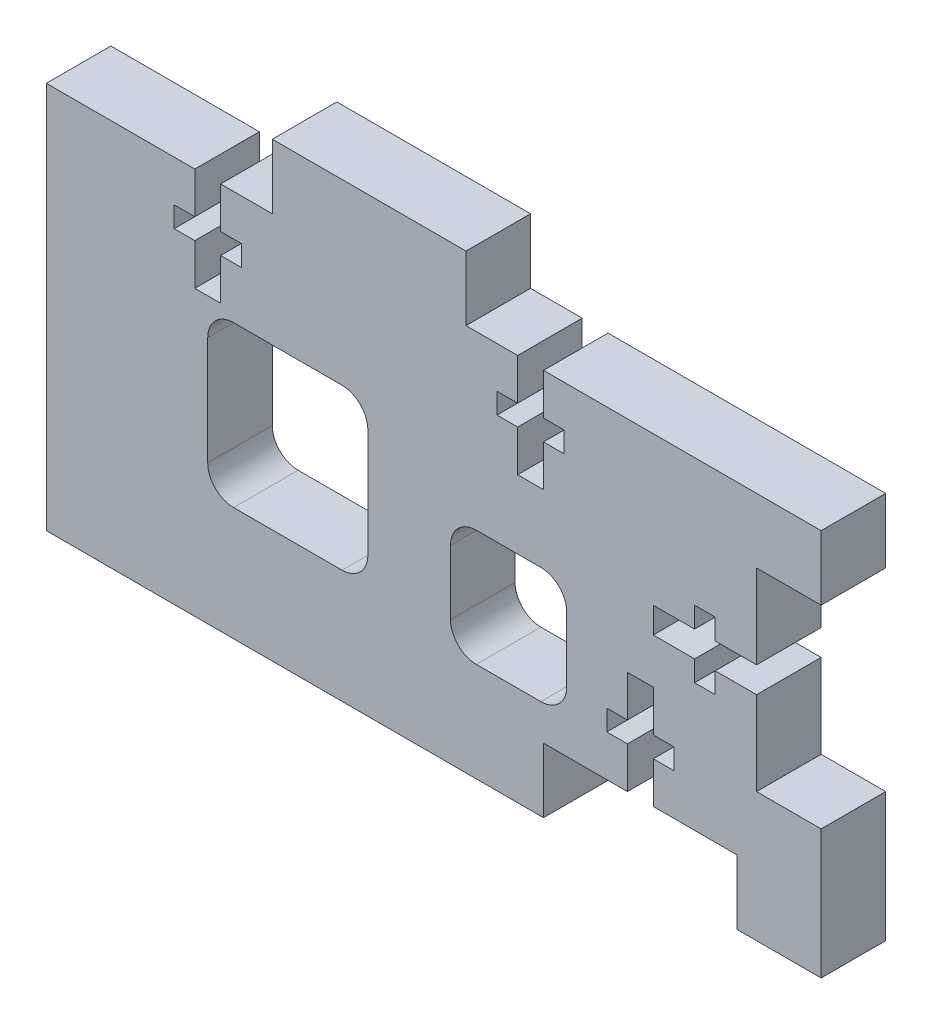
SolidWorks part; units mm, degrees
ref_plane "Front" through (0, 0, 0) normal (0, 0, 1) x (1, 0, 0)
ref_plane "Top" through (0, 0, 0) normal (0, 1, 0) x (1, 0, 0)
ref_plane "Right" through (0, 0, 0) normal (1, 0, 0) x (0, 0, -1)
sketch "Sketch1" plane through (0, 0, 0) normal (0, 0, 1) x (1, 0, 0)
  line L1 (-38.1, -15.875) -> (38.1, -15.875)
  line L2 (-38.1, -15.875) -> (-38.1, 15.875)
  line L3 (-38.1, 15.875) -> (38.1, 15.875)
  line L4 (38.1, -15.875) -> (38.1, 15.875)
  line L5 (-38.1, -15.875) -> (38.1, 15.875) construction
  line L6 (-38.1, 15.875) -> (38.1, -15.875) construction
  point P0 (0, 0)
  dimension "D1" = 31.75
  dimension "D2" = 76.2
extrude "Boss-Extrude1" add sketch "Sketch1" along normal blind 6.35
sketch "Sketch2" plane through (0, 0, 6.35) normal (0, 0, 1) x (1, 0, 0)
  line L0 (-38.1, 15.875) -> (-38.1, -15.875) construction
  line L1 (-15.875, 15.875) -> (3.175, 15.875)
  line L2 (-15.875, 15.875) -> (-15.875, 22.225)
  line L3 (-15.875, 22.225) -> (3.175, 22.225)
  line L4 (3.175, 15.875) -> (3.175, 22.225)
  line L5 (-15.875, 15.875) -> (3.175, 22.225) construction
  line L6 (-15.875, 22.225) -> (3.175, 15.875) construction
  line L7 (38.1, 15.875) -> (-38.1, 15.875) construction
  point P0 (-6.35, 19.05)
  dimension "D1" = 19.05
  dimension "D2" = 6.35
  dimension "D3" = 31.75
extrude "Boss-Extrude2" add sketch "Sketch2" against normal up to surface (6.35 mm away) up to face at (0, 0, 0)
sketch "Sketch3" plane through (0, 0, 6.35) normal (0, 0, 1) x (1, 0, 0)
  line L0 (-6.35, 22.225) -> (-6.35, 15.7879) construction
  line L1 (3.175, 22.225) -> (-15.875, 22.225) construction
  line L2 (-15.875, 19.05) -> (3.175, 19.05) construction
  line L3 (-15.875, 22.225) -> (-15.875, 15.875) construction
  line L4 (3.175, 15.875) -> (3.175, 22.225) construction
  line L5 (-20.955, 11.811) -> (-18.923, 11.811)
  line L6 (-23.495, 15.875) -> (-20.955, 15.875)
  line L7 (-23.495, 15.875) -> (-23.495, 11.811)
  line L8 (-23.495, 5.715) -> (-20.955, 5.715)
  line L9 (-20.955, 15.875) -> (-20.955, 11.811)
  line L10 (-23.495, 15.875) -> (-20.955, 5.715) construction
  line L11 (-23.495, 5.715) -> (-20.955, 15.875) construction
  line L12 (-25.527, 9.779) -> (-23.495, 9.779)
  line L13 (-25.527, 9.779) -> (-25.527, 11.811)
  line L14 (-25.527, 11.811) -> (-23.495, 11.811)
  line L15 (-18.923, 9.779) -> (-18.923, 11.811)
  line L16 (-25.527, 9.779) -> (-18.923, 11.811) construction
  line L17 (-25.527, 11.811) -> (-18.923, 9.779) construction
  line L18 (-20.955, 9.779) -> (-18.923, 9.779)
  line L19 (-23.495, 9.779) -> (-23.495, 5.715)
  line L20 (-20.955, 9.779) -> (-20.955, 5.715)
  line L21 (-15.875, 15.875) -> (-38.1, 15.875) construction
  line L22 (12.827, 11.811) -> (6.223, 9.779) construction
  line L23 (12.827, 9.779) -> (6.223, 11.811) construction
  line L24 (10.795, 5.715) -> (8.255, 15.875) construction
  line L25 (10.795, 15.875) -> (8.255, 5.715) construction
  line L26 (8.255, 9.779) -> (8.255, 5.715)
  line L27 (10.795, 9.779) -> (10.795, 5.715)
  line L28 (8.255, 9.779) -> (6.223, 9.779)
  line L29 (6.223, 9.779) -> (6.223, 11.811)
  line L30 (12.827, 11.811) -> (10.795, 11.811)
  line L31 (12.827, 9.779) -> (12.827, 11.811)
  line L32 (12.827, 9.779) -> (10.795, 9.779)
  line L33 (8.255, 15.875) -> (8.255, 11.811)
  line L34 (10.795, 5.715) -> (8.255, 5.715)
  line L35 (10.795, 15.875) -> (10.795, 11.811)
  line L36 (10.795, 15.875) -> (8.255, 15.875)
  line L37 (8.255, 11.811) -> (6.223, 11.811)
  point P10 (-22.225, 10.795)
  point P15 (-22.225, 10.795)
  point P38 (9.525, 10.795)
  dimension "D1" = 2.54
  dimension "D2" = 10.16
  dimension "D3" = 2.032
  dimension "D4" = 6.604
  dimension "D5" = 15.875
extrude "Cut-Extrude1" cut sketch "Sketch3" against normal up to surface (6.35 mm away) up to face at (0.3969, 9.525, 0)
sketch "Sketch4" plane through (0, 0, 6.35) normal (0, 0, 1) x (1, 0, 0)
  line L0 (38.1, -15.875) -> (38.1, 15.875) construction
  line L1 (38.1, 0) -> (-38.1, 0) construction
  line L3 (38.1, -15.875) -> (38.1, 15.875) construction
  line L4 (31.75, -9.525) -> (38.1, -9.525)
  line L5 (31.75, -9.525) -> (31.75, -1.27)
  line L6 (31.75, 9.525) -> (38.1, 9.525)
  line L7 (38.1, -9.525) -> (38.1, 9.525)
  line L8 (31.75, -9.525) -> (38.1, 9.525) construction
  line L9 (31.75, 9.525) -> (38.1, -9.525) construction
  line L10 (25.654, 1.27) -> (21.59, 1.27)
  line L11 (31.75, 1.27) -> (27.686, 1.27)
  line L12 (0, 0) -> (0, 22.225) construction
  line L13 (31.75, -1.27) -> (27.686, -1.27)
  line L14 (21.59, 1.27) -> (21.59, -1.27)
  line L15 (31.75, 1.27) -> (21.59, -1.27) construction
  line L16 (31.75, -1.27) -> (21.59, 1.27) construction
  line L17 (25.654, 3.302) -> (27.686, 3.302)
  line L18 (25.654, 3.302) -> (25.654, 1.27)
  line L19 (25.654, -3.302) -> (27.686, -3.302)
  line L20 (27.686, 3.302) -> (27.686, 1.27)
  line L21 (25.654, 3.302) -> (27.686, -3.302) construction
  line L22 (25.654, -3.302) -> (27.686, 3.302) construction
  line L23 (25.654, -1.27) -> (21.59, -1.27)
  line L24 (25.654, -1.27) -> (25.654, -3.302)
  line L25 (27.686, -1.27) -> (27.686, -3.302)
  line L26 (31.75, 1.27) -> (31.75, 9.525)
  line L27 (3.175, 22.225) -> (-15.875, 22.225) construction
  point P0 (38.1, 0)
  point P7 (34.925, 0)
  point P14 (26.67, 0)
  point P19 (26.67, 0)
  point P40 (-30.4006, -32.6246)
  dimension "D1" = 6.35
  dimension "D2" = 19.05
  dimension "D3" = 2.54
  dimension "D4" = 10.16
  dimension "D5" = 6.604
  dimension "D6" = 2.032
  dimension "D7" = 1.27
extrude "Cut-Extrude4" cut sketch "Sketch4" against normal up to surface (6.35 mm away) up to face at (-4.7427, 10.4775, 0)
sketch "Sketch5" plane through (0, 0, 6.35) normal (0, 0, 1) x (1, 0, 0)
  line L1 (-38.1, -15.875) -> (38.1, -15.875)
  line L2 (-38.1, -15.875) -> (-38.1, -22.225)
  line L3 (-38.1, -22.225) -> (38.1, -22.225)
  line L4 (38.1, -15.875) -> (38.1, -22.225)
  dimension "D1" = 6.35
extrude "Boss-Extrude3" add sketch "Sketch5" against normal up to surface (6.35 mm away) up to face at (6.4161, 6.985, 0)
sketch "Sketch6" plane through (0, 0, 6.35) normal (0, 0, 1) x (1, 0, 0)
  line L0 (-38.1, -22.225) -> (38.1, -22.225) construction
  line L1 (0, -22.225) -> (0, -1.6974) construction
  line L2 (-9.525, -22.225) -> (9.525, -22.225)
  line L3 (-9.525, -22.225) -> (-9.525, -15.875)
  line L4 (-9.525, -15.875) -> (-1.27, -15.875)
  line L5 (9.525, -22.225) -> (9.525, -15.875)
  line L6 (1.27, -15.875) -> (9.525, -15.875)
  line L7 (-1.27, -9.779) -> (-1.27, -5.715)
  line L8 (-1.27, -15.875) -> (-1.27, -11.811)
  line L9 (-1.27, -5.715) -> (1.27, -5.715)
  line L10 (1.27, -15.875) -> (1.27, -11.811)
  line L11 (-1.27, -15.875) -> (1.27, -5.715) construction
  line L12 (-1.27, -5.715) -> (1.27, -15.875) construction
  line L13 (-3.302, -11.811) -> (-1.27, -11.811)
  line L14 (-3.302, -11.811) -> (-3.302, -9.779)
  line L15 (-3.302, -9.779) -> (-1.27, -9.779)
  line L16 (3.302, -11.811) -> (3.302, -9.779)
  line L17 (-3.302, -11.811) -> (3.302, -9.779) construction
  line L18 (-3.302, -9.779) -> (3.302, -11.811) construction
  line L19 (1.27, -11.811) -> (3.302, -11.811)
  line L20 (1.27, -9.779) -> (1.27, -5.715)
  line L21 (1.27, -9.779) -> (3.302, -9.779)
  point P0 (0, -22.225)
  point P10 (0, -10.795)
  point P15 (0, -10.795)
  dimension "D1" = 19.05
  dimension "D2" = 6.35
  dimension "D3" = 9.525
  dimension "D4" = 10.16
  dimension "D5" = 2.54
  dimension "D6" = 2.032
  dimension "D7" = 6.604
extrude "Cut-Extrude5" [suppressed] cut sketch "Sketch6" against normal up to surface (6.35 mm away)
sketch "Sketch7" [suppressed] plane through (0, 0, 6.35) normal (0, 0, 1) x (1, 0, 0)
  line L0 (-3.302, -9.779) -> (-3.302, -11.811) construction
  line L1 (-31.7421, -12.928) -> (31.7421, -12.928) construction
  line L2 (-31.7421, -12.928) -> (-31.7421, 3.175) construction
  line L3 (-31.7421, 12.928) -> (31.7421, 12.928) construction
  line L4 (31.7421, -12.928) -> (31.7421, 12.928) construction
  line L5 (-31.7421, -12.928) -> (31.7421, 12.928) construction
  line L6 (-31.7421, 12.928) -> (31.7421, -12.928) construction
  line L7 (-8.382, -4.4173) -> (8.382, -4.4173)
  line L8 (8.255, 5.715) -> (10.795, 5.715) construction
  line L9 (-23.516, 3.175) -> (16.51, 3.175)
  line L10 (16.51, -2.2291) -> (16.51, 3.175)
  line L11 (-16.3971, -3.1533) -> (16.51, 3.175) construction
  line L12 (-23.516, 3.175) -> (16.51, -2.2291) construction
  line L14 (-31.7421, 3.175) -> (-31.7421, -12.928)
  line L15 (-31.7421, -12.928) -> (-8.382, -12.928)
  line L16 (-8.382, -4.4173) -> (-8.382, -12.928)
  line L17 (16.51, -2.2291) -> (16.51, -12.928)
  line L18 (16.51, -12.928) -> (8.382, -12.928)
  line L19 (8.382, -4.4173) -> (8.382, -12.928)
  line L20 (3.302, -11.811) -> (3.302, -9.779) construction
  line L21 (21.59, 1.27) -> (21.59, -1.27) construction
  line L22 (-23.516, 3.175) -> (-31.7421, 3.175)
  line L23 (-31.7421, 4.7625) -> (-31.7421, 12.928) construction
  point P0 (0, 0)
  point P6 (0, 0)
  point P11 (-31.7421, 4.7625)
  point P12 (-23.516, 3.175)
  dimension "D1" = 9.525
  dimension "D3" = 5.08
  dimension "D4" = 5.08
  dimension "D5" = 5.08
  dimension "D6" = 2.54
extrude "Cut-Extrude6" [suppressed] cut sketch "Sketch7" against normal up to surface (6.35 mm away)
sketch "Sketch8" plane through (0, 0, 6.35) normal (0, 0, 1) x (1, 0, 0)
  line L0 (-38.1, -22.225) -> (38.1, -22.225) construction
  line L1 (-19.685, 4.699) -> (-9.017, 4.699)
  line L2 (-22.225, 2.159) -> (-22.225, -8.509)
  line L3 (-19.685, -11.049) -> (-9.017, -11.049)
  line L4 (-6.477, 2.159) -> (-6.477, -8.509)
  line L5 (4.191, -1.0414) -> (10.541, -1.0414)
  line L6 (1.651, -3.5814) -> (1.651, -9.9314)
  line L7 (4.191, -12.4714) -> (10.541, -12.4714)
  line L8 (13.081, -3.5814) -> (13.081, -9.9314)
  line L9 (10.795, -22.225) -> (29.845, -22.225)
  line L10 (10.795, -22.225) -> (10.795, -15.875)
  line L11 (10.795, -15.875) -> (19.05, -15.875)
  line L12 (29.845, -22.225) -> (29.845, -15.875)
  line L15 (19.05, -15.875) -> (19.05, -11.811)
  line L16 (19.05, -5.715) -> (21.59, -5.715)
  line L17 (21.59, -15.875) -> (21.59, -11.811)
  line L18 (19.05, -9.779) -> (17.018, -9.779)
  line L20 (19.05, -11.811) -> (17.018, -11.811)
  line L21 (17.018, -9.779) -> (17.018, -11.811)
  line L22 (21.59, -9.779) -> (23.622, -9.779)
  line L23 (20.32, -15.875) -> (20.32, -22.225) construction
  line L24 (21.59, -11.811) -> (23.622, -11.811)
  line L25 (23.622, -9.779) -> (23.622, -11.811)
  line L26 (7.366, -1.0414) -> (7.366, -6.7564) construction
  line L27 (7.366, -6.7564) -> (7.366, -12.4714) construction
  line L28 (7.366, -6.7564) -> (1.651, -6.7564) construction
  line L29 (31.75, -1.27) -> (31.75, -9.525) construction
  line L30 (-22.225, -3.175) -> (-6.477, -3.175) construction
  line L31 (7.366, -6.7564) -> (13.081, -6.7564) construction
  line L33 (-18.923, 9.779) -> (-18.923, 11.811) construction
  line L34 (-25.527, 9.779) -> (-23.495, 9.779) construction
  line L35 (-23.495, 5.715) -> (-20.955, 5.715) construction
  line L36 (21.59, -9.779) -> (21.59, -5.715)
  line L37 (19.05, -9.779) -> (19.05, -5.715)
  line L38 (-20.955, 11.811) -> (-20.955, 15.875) construction
  line L39 (-20.955, 5.715) -> (-20.955, 9.779) construction
  line L42 (20.32, -15.875) -> (20.32, -5.715) construction
  line L43 (21.59, -15.875) -> (29.845, -15.875)
  arc A0 (1.651, -9.9314) -> (4.191, -12.4714) centre (4.191, -9.9314) ccw
  arc A1 (10.541, -12.4714) -> (13.081, -9.9314) centre (10.541, -9.9314) ccw
  arc A2 (10.541, -1.0414) -> (13.081, -3.5814) centre (10.541, -3.5814) cw
  arc A3 (4.191, -1.0414) -> (1.651, -3.5814) centre (4.191, -3.5814) ccw
  arc A4 (-22.225, -8.509) -> (-19.685, -11.049) centre (-19.685, -8.509) ccw
  arc A5 (-9.017, -11.049) -> (-6.477, -8.509) centre (-9.017, -8.509) ccw
  arc A6 (-9.017, 4.699) -> (-6.477, 2.159) centre (-9.017, 2.159) cw
  arc A7 (-19.685, 4.699) -> (-22.225, 2.159) centre (-19.685, 2.159) ccw
  point P58 (13.081, -1.0414)
  point P61 (1.651, -1.0414)
  point P64 (-22.225, -11.049)
  point P70 (-6.477, 4.699)
  point P73 (-22.225, 4.699)
  line M35 (-38.1, -22.225) -> (38.1, -22.225)
  dimension "D10" = 2.54
  dimension "D1" = 6.35
  dimension "D2" = 19.05
  dimension "D3" = 24.384
  dimension "D4" = 9.1186
  dimension "D5" = 11.43
  dimension "D6" = 15.748
  dimension "D7" = 4.826
  dimension "D8" = 53.975
  dimension "D9" = 15.748
  dimension "D11" = 11.43
extrude "Cut-Extrude7" cut sketch "Sketch8" against normal through all both and the other way through all contours L1 A7 L2 A4 L3 A5 L4 A6 | L43 L17 L24 L25 L22 L36 L16 L37 L18 L21 L20 L15 L11 L10 L12 M35 | L5 A3 L6 A0 L7 A1 L8 A2
